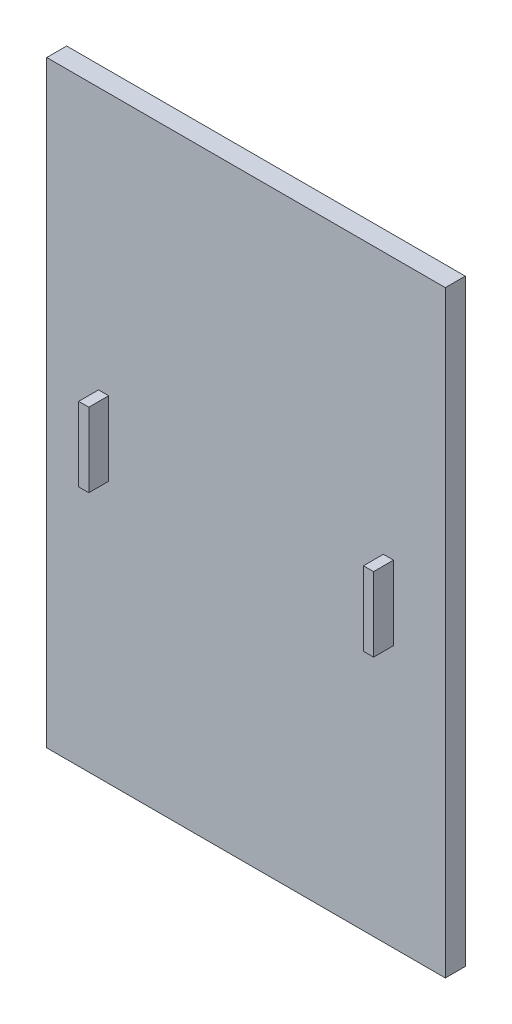
SolidWorks part; units mm, degrees
ref_plane "Front Plane" through (0, 0, 0) normal (0, 0, 1) x (1, 0, 0)
ref_plane "Top Plane" through (0, 0, 0) normal (0, 1, 0) x (1, 0, 0)
ref_plane "Right Plane" through (0, 0, 0) normal (1, 0, 0) x (0, 0, -1)
sketch "Sketch1" plane through (0, 0, 0) normal (0, 0, 1) x (1, 0, 0)
  line L1 (-50, 75) -> (50, 75)
  line L2 (-50, 75) -> (-50, -75)
  line L3 (-50, -75) -> (50, -75)
  line L4 (50, 75) -> (50, -75)
  line L5 (-50, 75) -> (50, -75) construction
  line L6 (-50, -75) -> (50, 75) construction
  point P0 (0, 0)
  dimension "D1" = 100
  dimension "D2" = 150
extrude "Boss-Extrude1" add sketch "Sketch1" along normal blind 5
sketch "Sketch2" plane through (0, 0, 5) normal (0, 0, 1) x (1, 0, 0)
  line L1 (-36.995, 9.2919) -> (-34.4518, 9.2919)
  line L2 (-36.995, 9.2919) -> (-36.995, -9.2919)
  line L3 (-36.995, -9.2919) -> (-34.4518, -9.2919)
  line L4 (-34.4518, 9.2919) -> (-34.4518, -9.2919)
  line L5 (-36.995, 9.2919) -> (-34.4518, -9.2919) construction
  line L6 (-36.995, -9.2919) -> (-34.4518, 9.2919) construction
  point P0 (-35.7234, 0)
extrude "Boss-Extrude2" add sketch "Sketch2" along normal blind 5
mirror "Mirror1" about plane through (0, 0, 0) normal (1, 0, 0) of "Boss-Extrude2"
